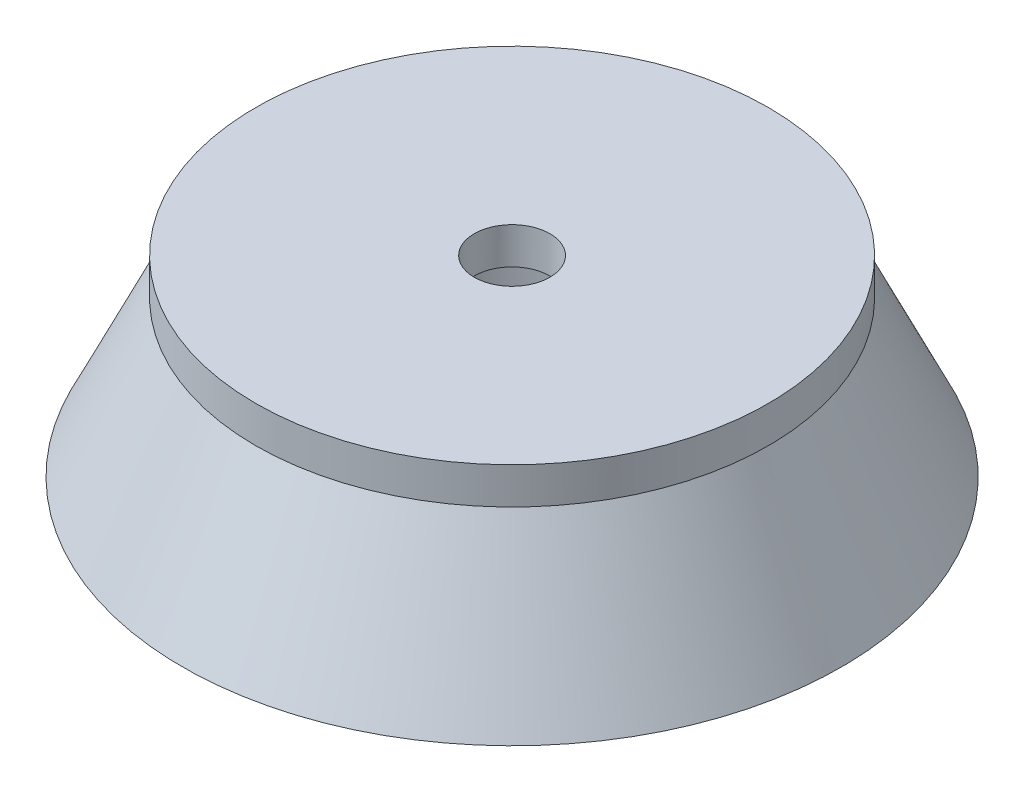
SolidWorks part; units mm, degrees
ref_plane "Alzado" through (0, 0, 0) normal (0, 0, 1) x (1, 0, 0)
ref_plane "Planta" through (0, 0, 0) normal (0, 1, 0) x (1, 0, 0)
ref_plane "Vista lateral" through (0, 0, 0) normal (1, 0, 0) x (0, 0, -1)
sketch "Croquis2" plane through (0, 0, 0) normal (0, 0, 1) x (1, 0, 0)
  line L0 (0, 0) -> (0, -38.0419) construction
  line L1 (0, -38.0419) -> (-45, -38.0419)
  line L2 (0, -16.8819) -> (-35, -16.8819)
  line L3 (-45, -38.0419) -> (-35, -16.8819)
  line L4 (0, -38.0419) -> (0, -16.8819)
  dimension "D1" = 45
  dimension "D2" = 35
  dimension "D3" = 21.16
revolve "Revolución1" add sketch "Croquis2" angle 360 about L0
sketch "Croquis3" plane through (0, -16.8819, 0) normal (0, 1, 0) x (1, 0, 0)
  circle A0 centre (0, 0) radius 35
extrude "Saliente-Extruir1" add sketch "Croquis3" along normal blind 5
sketch "Croquis4" plane through (0, -11.8819, 0) normal (0, 1, 0) x (1, 0, 0)
  circle A0 centre (0, 0) radius 5.16
  dimension "D1" = 10.32
extrude "Cortar-Extruir1" cut sketch "Croquis4" against normal through all
sketch "Croquis5" plane through (0, -38.0419, 0) normal (0, -1, 0) x (1, 0, 0)
  circle A0 centre (0, 0) radius 15
  dimension "D1" = 30
extrude "Cortar-Extruir2" cut sketch "Croquis5" against normal blind 21.16
sketch "Croquis6" plane through (0, -38.0419, 0) normal (0, -1, 0) x (1, 0, 0)
  line L1 (15, 0) -> (-15, 0)
  line L2 (-15, 0) -> (-15, -42.4264)
  line L3 (15, 0) -> (15, -42.4264)
  circle A0 centre (0, 0) radius 15 construction
  circle A1 centre (0, 0) radius 15 construction
  circle A2 centre (0, 0) radius 45 construction
  spline S0 degree 3 poles (-15, -42.4264) (-10.1981, -44.1276) (-0.0051, -45.873) (10.2038, -44.1264) (15, -42.4264) knots 0 0 0 0 0.500054 1 1 1 1
extrude "Cortar-Extruir4" cut sketch "Croquis6" against normal blind 5
